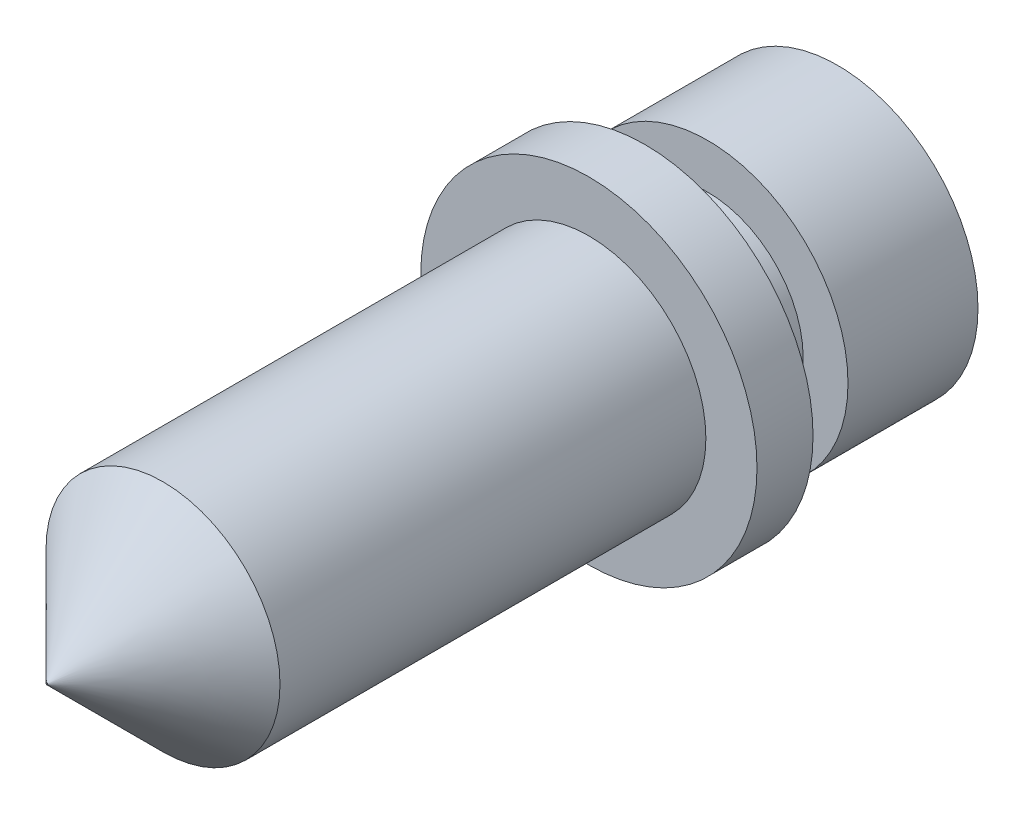
SolidWorks part; units mm, degrees
material "Brass"
ref_plane "Front Plane" through (0, 0, 0) normal (0, 0, 1) x (1, 0, 0)
ref_plane "Top Plane" through (0, 0, 0) normal (0, 1, 0) x (1, 0, 0)
ref_plane "Right Plane" through (0, 0, 0) normal (1, 0, 0) x (0, 0, -1)
sketch "Sketch1" plane through (0, 0, 0) normal (0, 0, 1) x (1, 0, 0)
  circle A0 centre (0, 0) radius 4.7625
  dimension "D1" = 9.525
extrude "Boss-Extrude1" add sketch "Sketch1" along normal mid plane 1.5875
sketch "Sketch2" plane through (0, 0, -0.7937) normal (0, 0, -1) x (-1, 0, 0)
  circle A0 centre (0, 0) radius 3.9751
  dimension "D1" = 7.9502
extrude "Boss-Extrude2" add sketch "Sketch2" along normal blind 5.461
sketch "Sketch3" plane through (0, 0, 0.7937) normal (0, 0, 1) x (1, 0, 0)
  circle A0 centre (0, 0) radius 3.3147
  dimension "D1" = 6.6294
extrude "Boss-Extrude3" add sketch "Sketch3" along normal blind 12.065
sketch "Sketch4" plane through (0, 0, 0) normal (1, 0, 0) x (0, 0, -1)
  line L0 (0, 0) -> (-11.7022, 0) construction
sketch "Sketch5" plane through (0, 0, 0) normal (1, 0, 0) x (0, 0, -1)
  line L0 (-12.8587, 3.3147) -> (-16.1734, 0)
  line L1 (0, 0) -> (-11.7022, 0) construction
  line L2 (-16.1734, 0) -> (-12.8587, 0)
  line L3 (-12.8587, 3.3147) -> (-12.8587, -3.3147) construction
  line L4 (-12.8587, 0) -> (-12.8587, 3.3147)
  dimension "D1" = 45
revolve "Revolve1" add sketch "Sketch5" angle 360 about L0
sketch "Sketch6" plane through (0, 0, -6.2547) normal (0, 0, -1) x (-1, 0, 0)
  circle A0 centre (0, 0) radius 1.5875
  dimension "D1" = 3.175
extrude "Cut-Extrude1" cut sketch "Sketch6" against normal blind 19.05
sketch "Sketch10" plane through (0, 0, 0) normal (0, 1, 0) x (1, 0, 0)
  line L0 (-3.9751, 6.2547) -> (-3.9751, 0.7938) construction
  line L1 (-3.9751, 0.7938) -> (-2.7051, 0.7938)
  line L2 (-3.9751, 0.7938) -> (-3.9751, 2.5718)
  line L3 (-3.9751, 2.5718) -> (-2.7051, 2.5718)
  line L4 (-2.7051, 0.7938) -> (-2.7051, 2.5718)
  line L5 (3.9751, 0.7938) -> (-3.9751, 0.7938) construction
  line L6 (0, 0) -> (0, 6.2547) construction
  line L7 (1.5875, 6.2547) -> (-1.5875, 6.2547) construction
  dimension "D1" = 1.778
  dimension "D2" = 1.27
revolve "Cut-Revolve1" cut sketch "Sketch10" angle 360 about L6
ref_plane "Plane2" through (0, 0, 16.1734) normal (0, 0, 1) x (1, 0, 0)
sketch "Sketch11" plane through (0, 0, 16.1734) normal (0, 0, 1) x (1, 0, 0)
  circle A0 centre (0, 0) radius 0.0508
extrude "Cut-Extrude3" cut sketch "Sketch11" against normal blind 0.0254
sketch "Sketch9" plane through (0, 0, -6.2547) normal (0, 0, -1) x (-1, 0, 0)
  circle A0 centre (0, 0) radius 0.02
  dimension "D1" = 0.04
extrude "Cut-Extrude2" cut sketch "Sketch9" against normal through all
chamfer "Chamfer1" distance 1.27 angle 45 1 edges at (-1.5875, 0, -6.2547)
